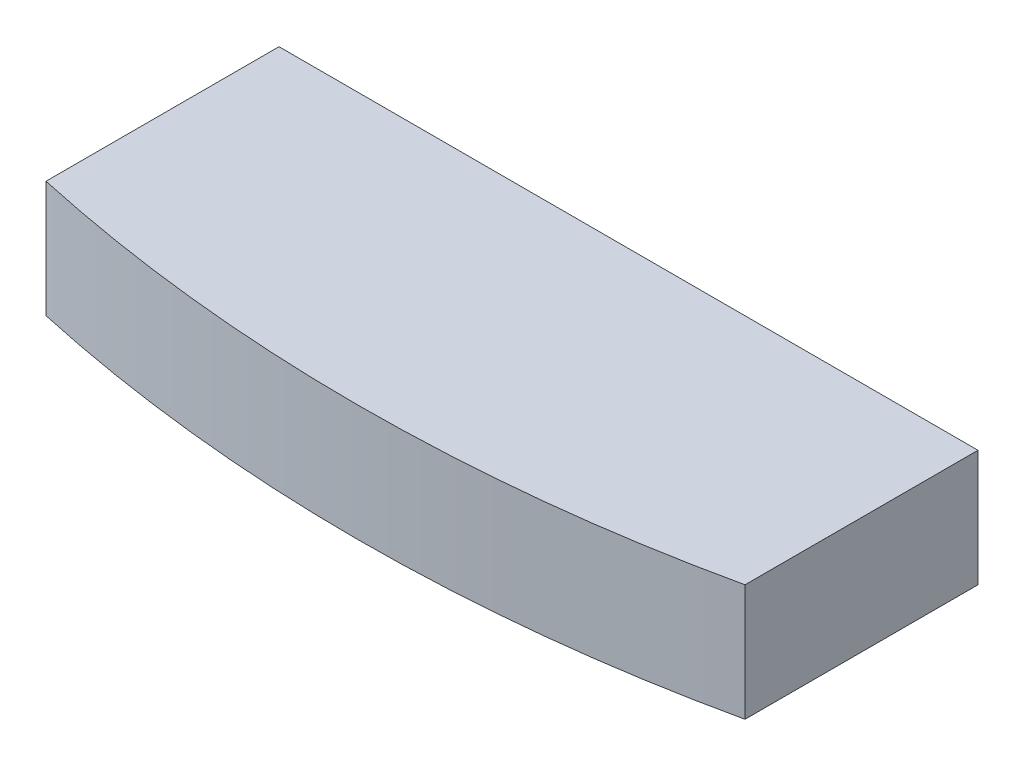
SolidWorks part; units mm, degrees
material "6061 Alloy"
ref_plane "Front Plane" through (0, 0, 0) normal (0, 0, 1) x (1, 0, 0)
ref_plane "Top Plane" through (0, 0, 0) normal (0, 1, 0) x (1, 0, 0)
ref_plane "Right Plane" through (0, 0, 0) normal (1, 0, 0) x (0, 0, -1)
sketch "Sketch1" plane through (0, 0, 0) normal (0, 1, 0) x (1, 0, 0)
  line L0 (-38.1, -173.4098) -> (-38.1, -148.0098)
  line L1 (-38.1, -148.0098) -> (0, -148.0098)
  line L4 (0, 0) -> (0, -177.546) construction
  line L5 (0, -148.0098) -> (0, -177.546)
  arc A1 (0, -177.546) -> (-38.1, -173.4098) centre (0, 0) cw
  dimension "D1" = 177.546
  dimension "D2" = 38.1
  dimension "D3" = 25.4
extrude "Boss-Extrude1" add sketch "Sketch1" along normal blind 12.7
mirror "Mirror1" about plane through (0, 12.7, 148.0098) normal (-1, 0, 0) of "Boss-Extrude1"
